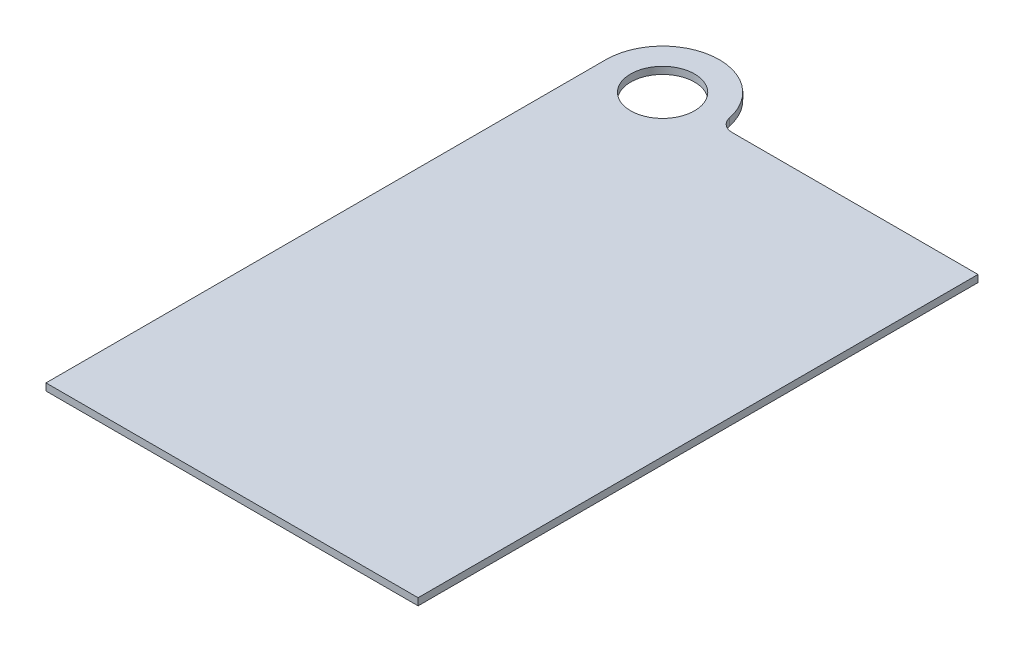
SolidWorks part; units mm, degrees
ref_plane "Front" through (0, 0, 0) normal (0, 0, 1) x (1, 0, 0)
ref_plane "Top" through (0, 0, 0) normal (0, 1, 0) x (1, 0, 0)
ref_plane "Right" through (0, 0, 0) normal (1, 0, 0) x (0, 0, -1)
sketch "Sketch1" plane through (0, 0, 0) normal (0, 1, 0) x (1, 0, 0)
  line L0 (-25.4, 0) -> (-25.4, -250.825)
  line L1 (-25.4, -250.825) -> (141.2875, -250.825)
  line L2 (141.2875, -250.825) -> (141.2875, 0)
  line L7 (25.4, 0) -> (141.2875, 0)
  line L8 (33.3375, 76.2) -> (134.9375, 76.2) construction
  line L9 (33.3375, 76.2) -> (33.3375, -225.425) construction
  line L10 (33.3375, -225.425) -> (134.9375, -225.425) construction
  line L11 (134.9375, 76.2) -> (134.9375, -225.425) construction
  line L12 (33.3375, 76.2) -> (134.9375, -225.425) construction
  line L13 (33.3375, -225.425) -> (134.9375, 76.2) construction
  circle A0 centre (0, 0) radius 14.3129
  arc A1 (25.4, 0) -> (-25.4, 0) centre (0, 0) ccw
  circle A2 centre (0, 0) radius 38.1 construction
  point P12 (84.1375, -74.6125)
  dimension "D1" = 28.6258
  dimension "D2" = 25.4
  dimension "D5" = 76.2
  dimension "D3" = 6.35
  dimension "D4" = 25.4
  dimension "D6" = 101.6
  dimension "D7" = 301.625
  dimension "D8" = 76.2
  dimension "D9" = 9.525
extrude "Boss-Extrude1" add sketch "Sketch1" along normal blind 3.175
fillet "Fillet2" radius 6.35 1 edges at (25.4, 1.5875, 0)
